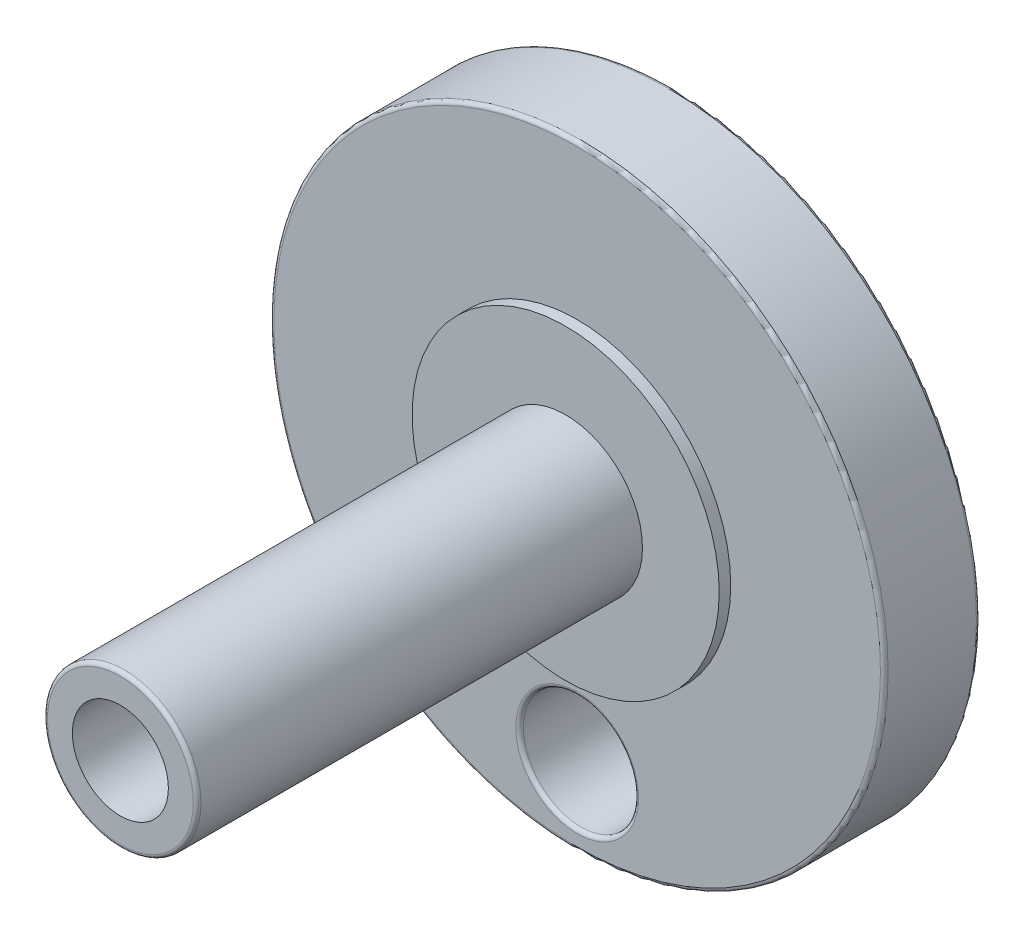
SolidWorks part; units mm, degrees
material "Stainless Steel (ferritic)"
ref_plane "Front Plane" through (0, 0, 0) normal (0, 0, 1) x (1, 0, 0)
ref_plane "Top Plane" through (0, 0, 0) normal (0, 1, 0) x (1, 0, 0)
ref_plane "Right Plane" through (0, 0, 0) normal (1, 0, 0) x (0, 0, -1)
sketch "Sketch1" plane through (0, 0, 0) normal (0, 0, 1) x (1, 0, 0)
  circle A0 centre (0, 0) radius 8
  dimension "D1" = 16
extrude "Boss-Extrude1" add sketch "Sketch1" along normal blind 2.5
sketch "Sketch3" plane through (0, 0, 2.5) normal (0, 0, 1) x (1, 0, 0)
  circle A0 centre (0, 0) radius 4
  dimension "D1" = 8
extrude "Boss-Extrude2" add sketch "Sketch3" along normal blind 0.3
sketch "Sketch4" plane through (0, 0, 2.8) normal (0, 0, 1) x (1, 0, 0)
  circle A0 centre (0, 0) radius 2
  dimension "D1" = 4
extrude "Boss-Extrude3" add sketch "Sketch4" along normal blind 11.6
sketch "Sketch5" plane through (0, 0, 14.4) normal (0, 0, 1) x (1, 0, 0)
  point P0 (0, 0)
hole_wizard "M3x0.5 Tapped Hole1" positions "Sketch5" profile "Sketch6" tap size "M3x0.5" standard "ANSI Metric"
sketch "Sketch6" plane through (0, 0, 14.4) normal (1, 0, 0) x (0, -1, 0)
  line L0 (0, 0) -> (0, 9.2511)
  line L1 (0, 9.2511) -> (1.25, 8.5)
  line L2 (1.25, 8.5) -> (1.25, 0)
  line L5 (1.25, 0) -> (0, 0)
  line L10 (0, 9.2511) -> (-1.25, 8.5) construction
  line L11 (0, -6.35) -> (0, 107.95) construction
  dimension "Tap Drill Dia." = 2.5
  dimension "Tap Drill Depth" = 8.5
  dimension "Drill Angle" = 118
cosmetic thread "Hole Thread1" parameters "D1"=7, "D2"=3
sketch "Sketch7" plane through (0, 0, 2.5) normal (0, 0, 1) x (1, 0, 0)
  circle A0 centre (0, -6) radius 1.5
  dimension "D1" = 3
  dimension "D2" = 6
extrude "Cut-Extrude1" cut sketch "Sketch7" against normal through all both and the other way through all
fillet "Fillet1" radius 0.1 5 edges at (1.5, -6, 2.5) (2, 0, 14.4) (1.5, -6, 0) (8, 0, 0) (8, 0, 2.5)
